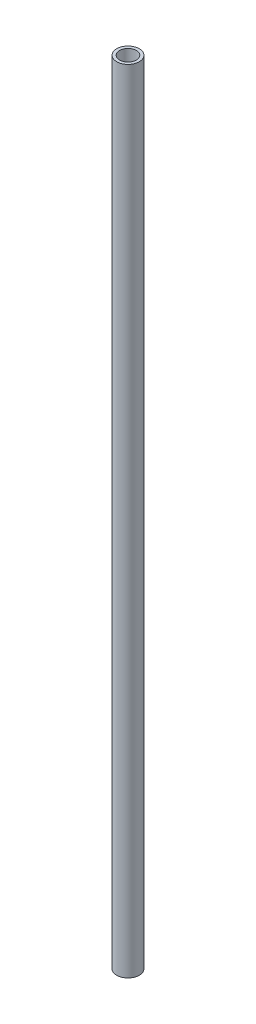
SolidWorks part; units mm, degrees
ref_plane "Front Plane" through (0, 0, 0) normal (0, 0, 1) x (1, 0, 0)
ref_plane "Top Plane" through (0, 0, 0) normal (0, 1, 0) x (1, 0, 0)
ref_plane "Right Plane" through (0, 0, 0) normal (1, 0, 0) x (0, 0, -1)
sketch "Sketch1" plane through (0, 0, 0) normal (0, 1, 0) x (1, 0, 0)
  circle A0 centre (0, 0) radius 7.8994
  circle A1 centre (0, 0) radius 10.668
  dimension "D1" = 15.7988
  dimension "D2" = 21.336
extrude "Boss-Extrude1" add sketch "Sketch1" along normal blind 748
